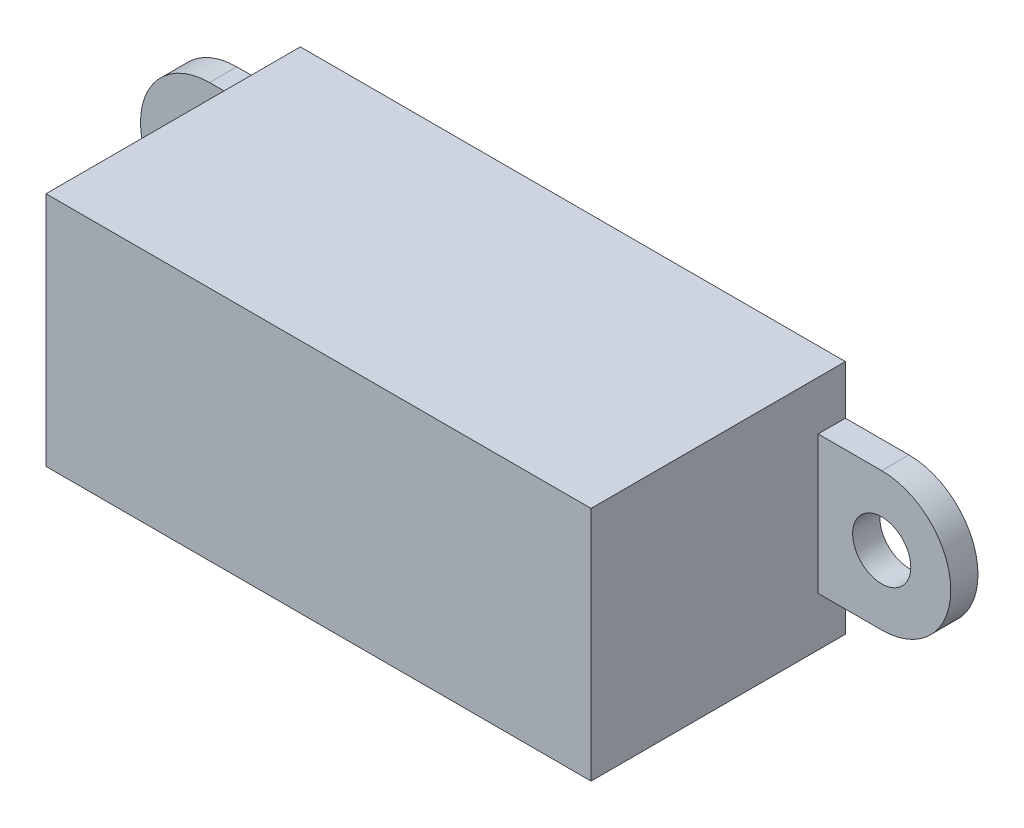
SolidWorks part; units mm, degrees
ref_plane "Front Plane" through (0, 0, 0) normal (0, 0, 1) x (1, 0, 0)
ref_plane "Top Plane" through (0, 0, 0) normal (0, 1, 0) x (1, 0, 0)
ref_plane "Right Plane" through (0, 0, 0) normal (1, 0, 0) x (0, 0, -1)
sketch "Sketch1" plane through (0, 0, 0) normal (0, 0, 1) x (1, 0, 0)
  line L1 (15, 6.5) -> (-15, 6.5)
  line L2 (15, 6.5) -> (15, -6.5)
  line L3 (15, -6.5) -> (-15, -6.5)
  line L4 (-15, 6.5) -> (-15, -6.5)
  line L5 (15, 6.5) -> (-15, -6.5) construction
  line L6 (15, -6.5) -> (-15, 6.5) construction
  point P0 (0, 0)
  dimension "D1" = 30
  dimension "D2" = 13
extrude "Boss-Extrude1" add sketch "Sketch1" along normal blind 14
sketch "Sketch2" plane through (0, 0, 0) normal (0, 0, 1) x (1, 0, 0)
  line L0 (15, -3.8) -> (15, 3.8)
  line L1 (15, -6.5) -> (15, 6.5) construction
  line L2 (15, 3.8) -> (18.5, 3.8)
  line L3 (15, -3.8) -> (18.5, -3.8)
  line L4 (0, 0) -> (50000, 0) construction
  arc A0 (18.5, -3.8) -> (18.5, 3.8) centre (18.5, 0) ccw
  circle A1 centre (18.5, 0) radius 1.6
  dimension "D1" = 3.8
  dimension "D3" = 3.2
  dimension "D2" = 18.5
extrude "Boss-Extrude2" add sketch "Sketch2" along normal blind 1.5
mirror "Mirror1" about plane through (0, 0, 0) normal (1, 0, 0) of "Boss-Extrude2"
